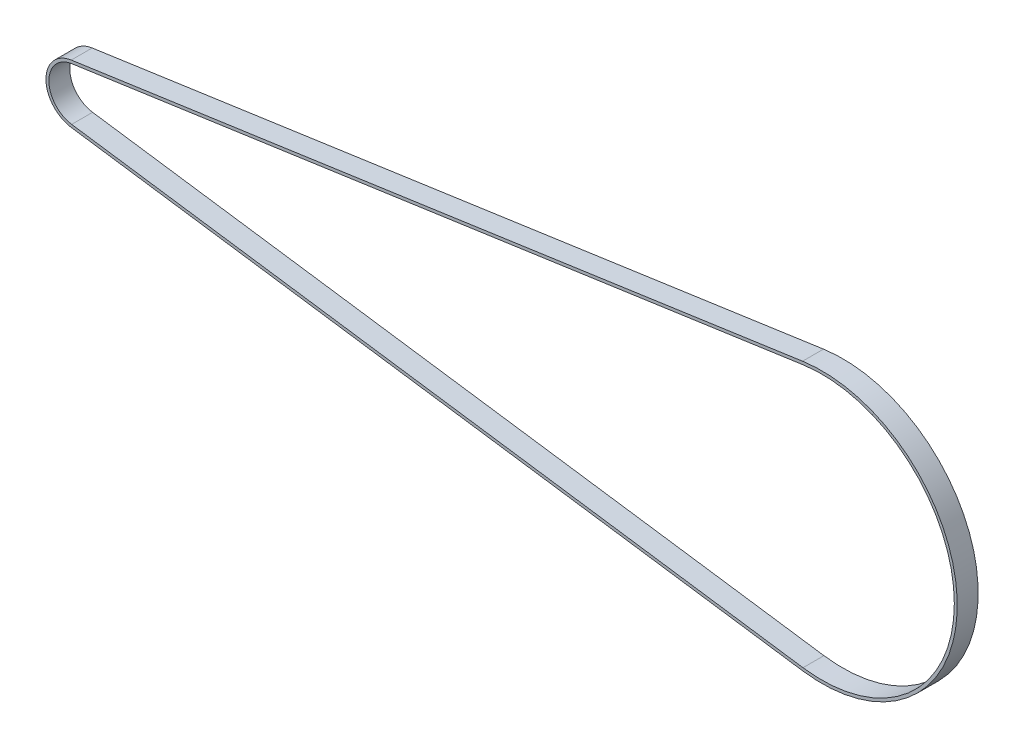
SolidWorks part; units mm, degrees
ref_plane "Front Plane" through (0, 0, 0) normal (0, 0, 1) x (1, 0, 0)
ref_plane "Top Plane" through (0, 0, 0) normal (0, 1, 0) x (1, 0, 0)
ref_plane "Right Plane" through (0, 0, 0) normal (1, 0, 0) x (0, 0, -1)
sketch "Sketch2" plane through (0, 0, 0) normal (0, 0, 1) x (1, 0, 0)
  line L0 (0, 0) -> (1, 0) construction
  line L1 (0, 0) -> (0, 1) construction
  line L2 (-2.5778, 17.9771) -> (497.1471, 89.6342)
  line L3 (497.1471, -89.6342) -> (-2.5778, -17.9771)
  arc A0 (-2.5778, -17.9771) -> (-2.5778, 17.9771) centre (0, 0) cw
  arc A1 (497.1471, 89.6342) -> (497.1471, -89.6342) centre (510, 0) cw
extrude "Extrude-Thin1" add sketch "Sketch2" along normal up to surface (14.3002 mm away) thin thin type one direction wall 2
